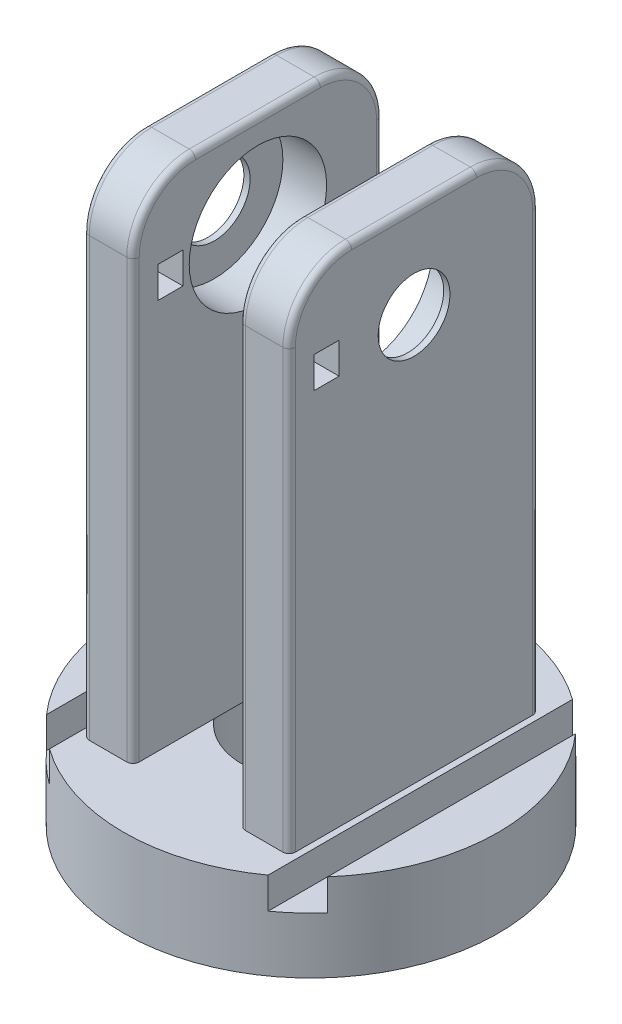
SolidWorks part; units mm, degrees
material "6061 Alloy"
ref_plane "Front Plane" through (0, 0, 0) normal (0, 0, 1) x (1, 0, 0)
ref_plane "Top Plane" through (0, 0, 0) normal (0, 1, 0) x (1, 0, 0)
ref_plane "Right Plane" through (0, 0, 0) normal (1, 0, 0) x (0, 0, -1)
sketch "Sketch1" plane through (0, 0, 0) normal (0, 1, 0) x (1, 0, 0)
  circle A0 centre (0, 0) radius 30
  dimension "D1" = 60
extrude "Boss-Extrude1" add sketch "Sketch1" along normal blind 14
sketch "Sketch2" plane through (0, 0, 0) normal (0, -1, 0) x (1, 0, 0)
  circle A0 centre (0, 0) radius 11.05
  dimension "D1" = 22.1
extrude "Cut-Extrude1" cut sketch "Sketch2" against normal through all
sketch "Sketch5" plane through (0, 14, 0) normal (0, 1, 0) x (1, 0, 0)
  line L0 (0, 0) -> (-8.5, 0) construction
  line L1 (0, 0) -> (8.5, 0) construction
  line L2 (-8.5, -20) -> (-8.5, 20)
  line L3 (-8.5, 20) -> (-16.5, 20)
  line L4 (-16.5, 20) -> (-16.5, -20)
  line L5 (-16.5, -20) -> (-8.5, -20)
  line L7 (16.5, -20) -> (16.5, 20)
  line L8 (16.5, 20) -> (8.5, 20)
  line L9 (8.5, 20) -> (8.5, -20)
  line L10 (8.5, -20) -> (16.5, -20)
  dimension "D1" = 8.5
  dimension "D2" = 8.5
  dimension "D3" = 8
  dimension "D4" = 20
  dimension "D5" = 20
  dimension "D6" = 0
  dimension "D7" = 8
  dimension "D8" = 20
  dimension "D9" = 20
extrude "Boss-Extrude2" add sketch "Sketch5" along normal blind 80
fillet "Fillet1" radius 10 4 edges at (-12.5, 94, -20) (12.5, 94, -20) (12.5, 94, 20) (-12.5, 94, 20)
sketch "Sketch12" plane through (0, 0, 0) normal (1, 0, 0) x (0, 0, -1)
  line L0 (-20, 84) -> (-20, 14) construction
  line L1 (-10, 94) -> (10, 94) construction
  circle A0 centre (0, 79) radius 11
  dimension "D1" = 22
  dimension "D2" = 20
  dimension "D3" = 15
extrude "Cut-Extrude5" cut sketch "Sketch12" against normal offset from surface 1 and the other way offset from surface (15.5 mm away) 1 up to face at (-16.5, 64.6904, 0) other way up to face at (16.5, 64.6904, 0)
sketch "Sketch13" plane through (-16.5, 0, 0) normal (-1, 0, 0) x (0, 0, 1)
  line L0 (-10, 94) -> (10, 94) construction
  line L1 (-20, 84) -> (-20, 14) construction
  circle A0 centre (0, 79) radius 5.75
  dimension "D1" = 11.5
  dimension "D2" = 15
  dimension "D3" = 20
extrude "Cut-Extrude6" cut sketch "Sketch13" against normal up to surface (33 mm away) up to face at (16.5, 64.6904, 0)
sketch "Sketch14" plane through (0, 14, 0) normal (0, 1, 0) x (1, 0, 0)
  line L0 (20, 0) -> (-20, 0) construction
  line L2 (-17.5, -30.05) -> (-22.5, -30.05)
  line L3 (-17.5, -30.05) -> (-17.5, 30.05)
  line L4 (-17.5, 30.05) -> (-22.5, 30.05)
  line L5 (-22.5, -30.05) -> (-22.5, 30.05)
  line L6 (-17.5, -30.05) -> (-22.5, 30.05) construction
  line L7 (-17.5, 30.05) -> (-22.5, -30.05) construction
  line L8 (17.5, -30.05) -> (22.5, -30.05)
  line L9 (17.5, -30.05) -> (17.5, 30.05)
  line L10 (17.5, 30.05) -> (22.5, 30.05)
  line L11 (22.5, -30.05) -> (22.5, 30.05)
  line L12 (17.5, -30.05) -> (22.5, 30.05) construction
  line L13 (17.5, 30.05) -> (22.5, -30.05) construction
  point P4 (0, 0)
  dimension "D1" = 40
  dimension "D2" = 5
  dimension "D3" = 60.1
  dimension "D4" = 5
  dimension "D5" = 60.1
extrude "Cut-Extrude7" cut sketch "Sketch14" against normal blind 5
fillet "Fillet2" radius 1 10 edges at (16.5, 49, 20) (16.5, 91.0711, 17.0711) (16.5, 94, 0) (16.5, 91.0711, -17.0711) (16.5, 49, -20) (-16.5, 49, 20) (-16.5, 91.0711, 17.0711) (-16.5, 94, 0) (-16.5, 91.0711, -17.0711) (-16.5, 49, -20)
fillet "Fillet3" radius 1 10 edges at (-8.5, 49, 20) (-8.5, 91.0711, 17.0711) (-8.5, 94, 0) (-8.5, 91.0711, -17.0711) (8.5, 49, 20) (8.5, 91.0711, 17.0711) (8.5, 94, 0) (8.5, 91.0711, -17.0711) (-8.5, 49, -20) (8.5, 49, -20)
sketch "Sketch15" plane through (16.5, 0, 0) normal (1, 0, 0) x (0, 0, -1)
  line L0 (0, 79) -> (-14, 79) construction
  line L2 (-16, 76.5) -> (-12, 76.5)
  line L3 (-16, 76.5) -> (-16, 81.5)
  line L4 (-16, 81.5) -> (-12, 81.5)
  line L5 (-12, 76.5) -> (-12, 81.5)
  line L6 (-16, 76.5) -> (-12, 81.5) construction
  line L7 (-16, 81.5) -> (-12, 76.5) construction
  dimension "D1" = 14
  dimension "D2" = 4
  dimension "D3" = 5
extrude "Cut-Extrude14" cut sketch "Sketch15" against normal up to surface (33 mm away) up to face at (-16.5, 79, 5.75)
